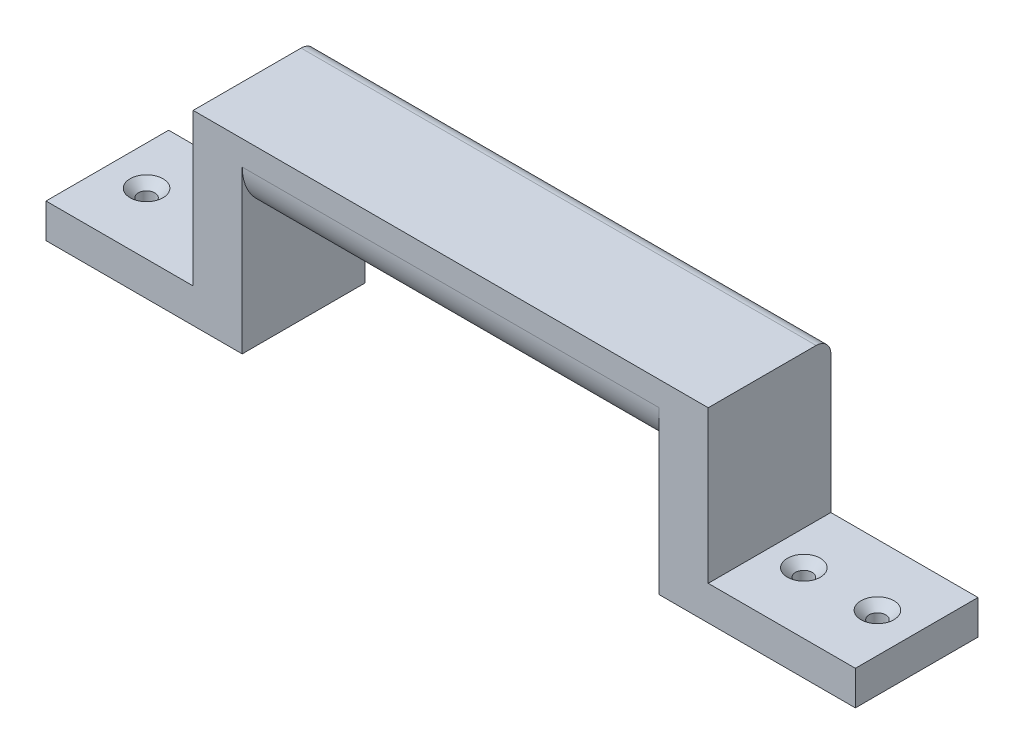
SolidWorks part; units mm, degrees
ref_plane "Alzado" through (0, 0, 0) normal (0, 0, 1) x (1, 0, 0)
ref_plane "Planta" through (0, 0, 0) normal (0, 1, 0) x (1, 0, 0)
ref_plane "Vista lateral" through (0, 0, 0) normal (1, 0, 0) x (0, 0, -1)
sketch "Croquis1" plane through (0, 0, 0) normal (0, 0, 1) x (1, 0, 0)
  line L0 (-96.5219, -23.6427) -> (-136.5219, -23.6427)
  line L1 (-136.5219, -23.6427) -> (-136.5219, -14.6427)
  line L2 (-136.5219, -14.6427) -> (-106.5219, -14.6427)
  line L3 (-106.5219, -14.6427) -> (-106.5219, 16.3573)
  line L4 (-106.5219, 16.3573) -> (-1.5219, 16.3573)
  line L5 (-1.5219, 16.3573) -> (-1.5219, -14.6427)
  line L6 (-1.5219, -14.6427) -> (28.4781, -14.6427)
  line L7 (28.4781, -14.6427) -> (28.4781, -23.6427)
  line L8 (28.4781, -23.6427) -> (-11.5219, -23.6427)
  line L9 (-11.5219, -23.6427) -> (-11.5219, 1.3573)
  line L10 (-11.5219, 1.3573) -> (-96.5219, 1.3573)
  line L11 (-96.5219, 1.3573) -> (-96.5219, -23.6427)
extrude "Saliente-Extruir1" add sketch "Croquis1" along normal blind 25
fillet "Redondeo1" radius 10 2 edges at (-54.0219, 1.3573, 0) (-54.0219, 1.3573, 25)
fillet "Redondeo2" radius 3 1 edges at (-54.0219, 16.3573, 0)
sketch "Croquis2" plane through (0, -14.6427, 0) normal (0, 1, 0) x (1, 0, 0)
  line L0 (-136.5219, -25) -> (-136.5219, 0) construction
  line L1 (-106.5219, 0) -> (-136.5219, 0) construction
  circle A0 centre (-113.5219, -12.5) radius 1.5
  circle A1 centre (-128.5219, -12.5) radius 1.5
  circle A2 centre (20.4781, -12.5) radius 1.5
  circle A3 centre (5.4781, -12.5) radius 1.5
  point P4 (-136.5219, -12.5)
  dimension "D1" = 8
  dimension "D2" = 12.5
  dimension "D3" = 12.5
  dimension "D4" = 15
  dimension "D5" = 2
extrude "Cortar-Extruir1" cut sketch "Croquis2" against normal up to vertex (9 mm away)
hole_wizard "Refrentado para tornillo tapón con cabeza plana de clavija de M31" positions "Croquis4" profile "Croquis3" countersink size "M3" standard "Ansi Metric" end condition through all
sketch "Croquis4" plane through (0, -14.6427, 0) normal (0, 1, 0) x (1, 0, 0)
  point P0 (-128.5219, -12.5)
  point P3 (-113.5219, -12.5)
  point P6 (20.4781, -12.5)
  point P9 (5.4781, -12.5)
sketch "Croquis3" plane through (-128.5219, -14.6427, 12.5) normal (1, 0, 0) x (0, 0, 1)
  line L0 (0, 0) -> (0, 9)
  line L1 (0, 9) -> (1.7, 9)
  line L2 (1.7, 9) -> (1.7, 1.66)
  line L3 (1.7, 1.66) -> (3.36, 0)
  line L5 (3.36, 0) -> (0, 0)
  line L6 (-1.7, 1.66) -> (-3.36, 0) construction
  line L11 (0, -6.35) -> (0, 107.95) construction
  dimension "Diámetro de taladro hasta el siguiente" = 3.4
  dimension "Profundidad de taladro hasta el siguiente" = 9
  dimension "Diámetro de avellanado cercano" = 6.72
  dimension "Ángulo de avellanado cercano" = 90
sketch "Croquis5" plane through (0, 0, 25) normal (0, 0, 1) x (1, 0, 0)
  line L0 (-96.5219, -23.6427) -> (-96.5219, 11.3573) construction
  line L1 (-136.5219, -23.6427) -> (-96.5219, -23.6427)
  line L2 (-136.5219, -23.6427) -> (-136.5219, -21.6427)
  line L3 (-136.5219, -21.6427) -> (-96.5219, -21.6427)
  line L4 (-96.5219, -23.6427) -> (-96.5219, -21.6427)
  line L5 (-11.5219, 11.3573) -> (-11.5219, -23.6427) construction
  line L6 (28.4781, -23.6427) -> (-11.5219, -23.6427)
  line L7 (28.4781, -23.6427) -> (28.4781, -21.6427)
  line L8 (28.4781, -21.6427) -> (-11.5219, -21.6427)
  line L9 (-11.5219, -23.6427) -> (-11.5219, -21.6427)
extrude "Cortar-Extruir2" cut sketch "Croquis5" against normal up to vertex (25 mm away)
